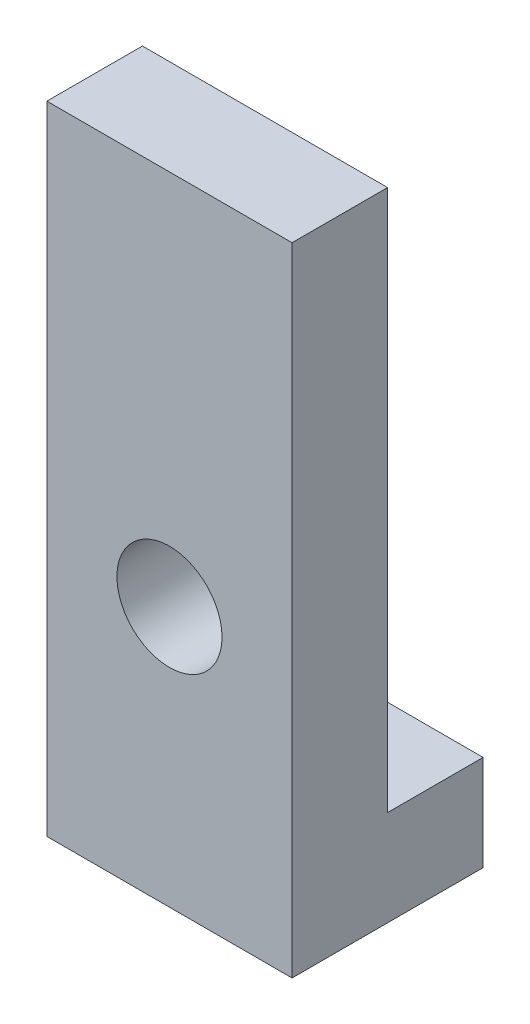
SolidWorks part; units mm, degrees
ref_plane "Front Plane" through (0, 0, 0) normal (0, 0, 1) x (1, 0, 0)
ref_plane "Top Plane" through (0, 0, 0) normal (0, 1, 0) x (1, 0, 0)
ref_plane "Right Plane" through (0, 0, 0) normal (1, 0, 0) x (0, 0, -1)
sketch "Sketch1" plane through (0, 0, 0) normal (0, 0, 1) x (1, 0, 0)
  line L0 (0, -20) -> (-24, -20) construction
  line L1 (-1.8, -20) -> (-9.5, -20)
  line L2 (-1.8, -20) -> (-1.8, -3)
  line L3 (-1.8, -3) -> (-9.5, -3)
  line L4 (-9.5, -20) -> (-9.5, -3)
  line L5 (0, -3) -> (-24, -3) construction
  line L6 (-12, -1020) -> (-12, 48980) construction
  line L7 (-5.65, -1014.8295) -> (-5.65, 48985.1705) construction
  circle A0 centre (-5.65, -14.8295) radius 1.65
  circle A1 centre (-5.65, -14.8295) radius 1.65 construction
  point P11 (-12, -20)
  dimension "D1" = 2.5
extrude "Boss-Extrude1" add sketch "Sketch1" along normal blind 3
sketch "Sketch2" plane through (0, -20, 0) normal (0, -1, 0) x (1, 0, 0)
  line L1 (-1.8, 3) -> (-9.5, 3)
  line L2 (-1.8, 3) -> (-1.8, -3)
  line L3 (-1.8, -3) -> (-9.5, -3)
  line L4 (-9.5, 3) -> (-9.5, -3)
  dimension "D1" = 6
extrude "Boss-Extrude2" add sketch "Sketch2" along normal blind 3
